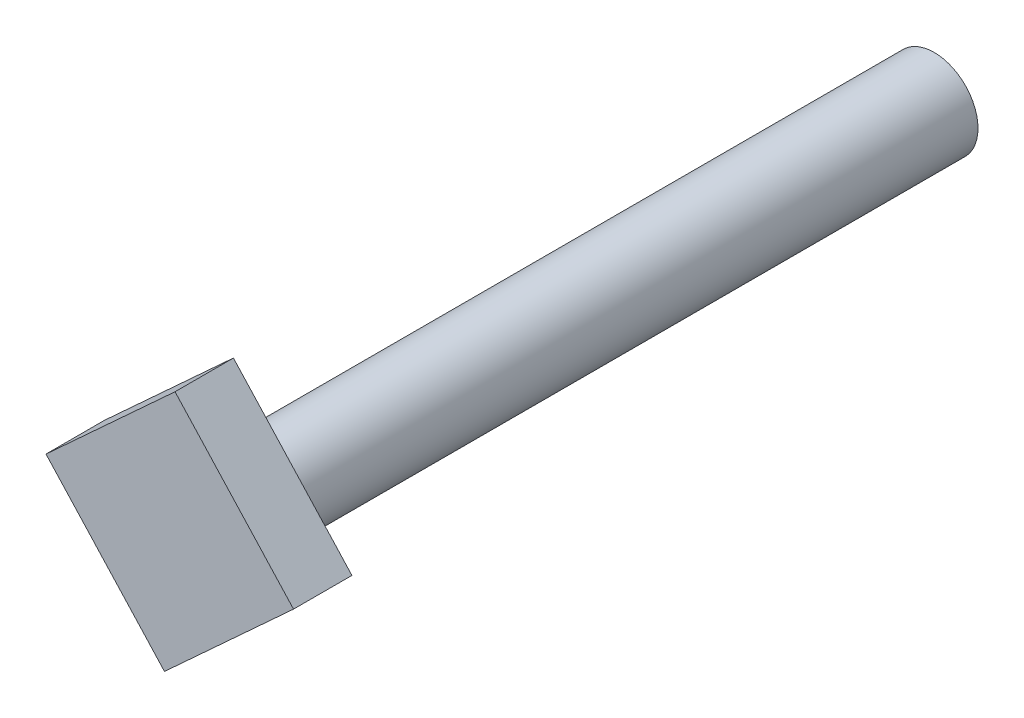
SolidWorks part; units mm, degrees
ref_plane "Front Plane" through (0, 0, 0) normal (0, 0, 1) x (1, 0, 0)
ref_plane "Top Plane" through (0, 0, 0) normal (0, 1, 0) x (1, 0, 0)
ref_plane "Right Plane" through (0, 0, 0) normal (1, 0, 0) x (0, 0, -1)
sketch "Sketch2" plane through (0, 0, 0) normal (0, 0, 1) x (1, 0, 0)
  line L0 (-11.9635, 13.0292) -> (11.9635, -13.0292) construction
  line L1 (-17.6781, 1.5104) -> (0, 17.7425)
  line L2 (-17.6781, 1.5104) -> (-1.446, -16.1678)
  line L3 (-1.446, -16.1678) -> (16.2322, 0.0644)
  line L4 (0, 17.7425) -> (16.2322, 0.0644)
  line L5 (0, 0) -> (0, 17.7425) construction
  point P0 (0, 0)
  point P4 (7.3931, -8.0517)
  point P5 (-8.8391, 9.6264)
  point P9 (0, 0)
  dimension "D1" = 24
  dimension "D2" = 42.558
extrude "Boss-Extrude1" add sketch "Sketch2" against normal blind 8
sketch "Sketch4" plane through (0, 0, 0) normal (0, 0, 1) x (1, 0, 0)
  circle A0 centre (0, 0) radius 6
  dimension "D1" = 12
extrude "Boss-Extrude2" add sketch "Sketch4" against normal blind 104
